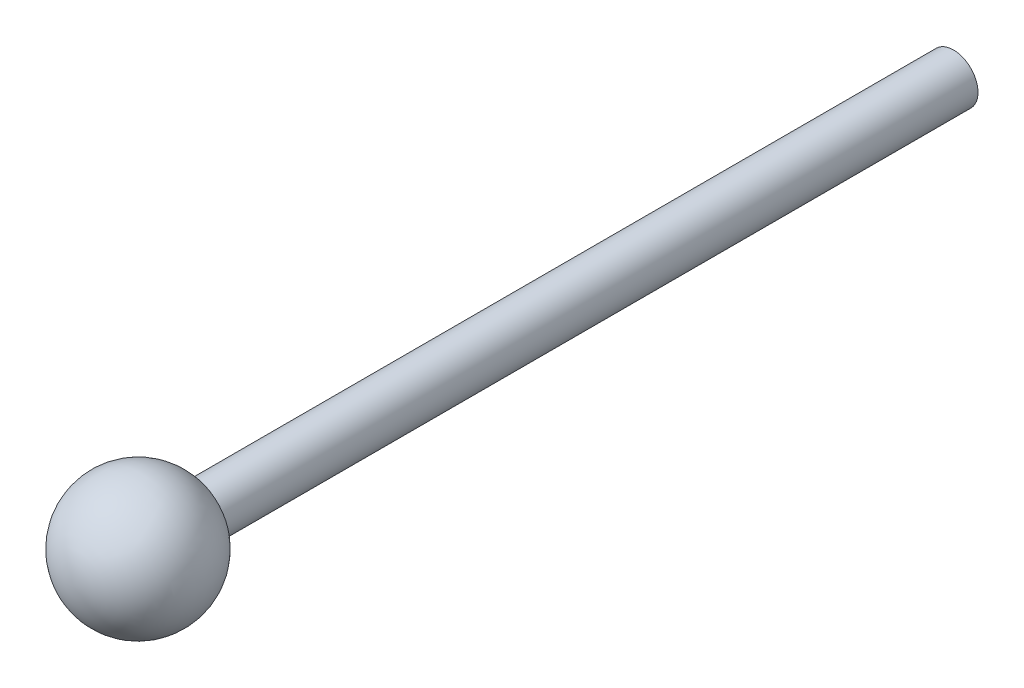
SolidWorks part; units mm, degrees
ref_plane "Front" through (0, 0, 0) normal (0, 0, 1) x (1, 0, 0)
ref_plane "Top" through (0, 0, 0) normal (0, 1, 0) x (1, 0, 0)
ref_plane "Right" through (0, 0, 0) normal (1, 0, 0) x (0, 0, -1)
sketch "Sketch1" plane through (0, 0, 0) normal (0, 0, 1) x (1, 0, 0)
  circle A0 centre (0, 0) radius 7.62
extrude "Base-Extrude" add sketch "Sketch1" against normal blind 254
sketch "Sketch5" plane through (0, 0, 0) normal (0, 0, 1) x (1, 0, 0)
  line L0 (0, 20.32) -> (0, -10.8337) construction
  line L1 (0, 20.32) -> (0, -20.32)
  arc A0 (0, 20.32) -> (0, -20.32) centre (0, 0) cw
revolve "Boss-Revolve1" add sketch "Sketch5" angle 360 about L0
